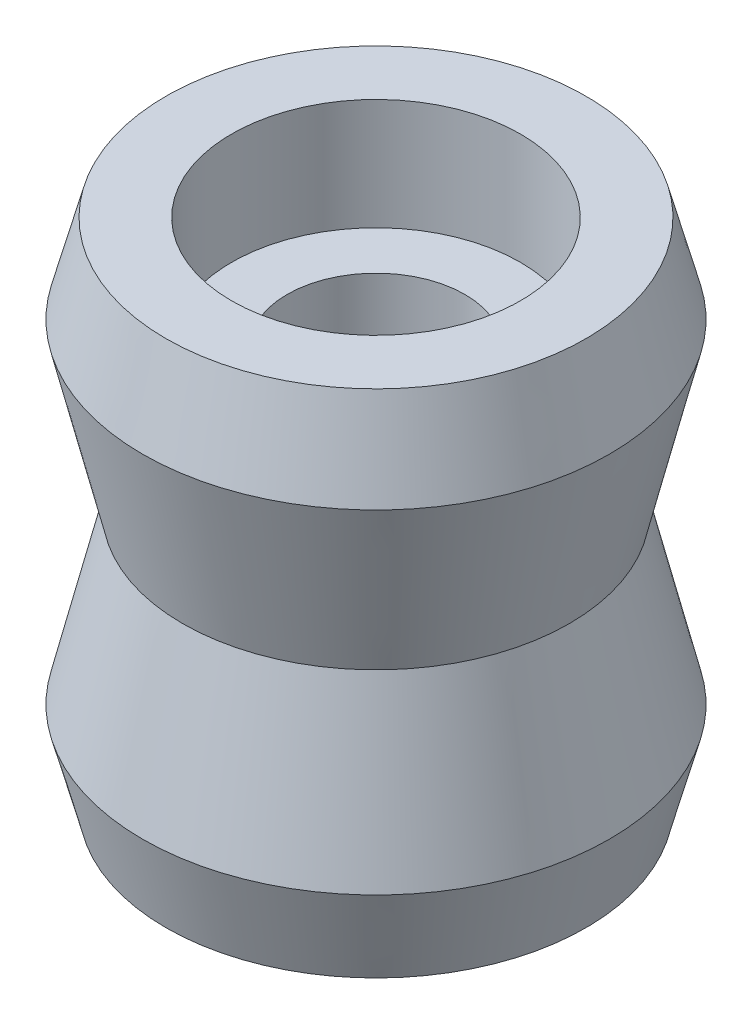
SolidWorks part; units mm, degrees
material "Maple"
ref_plane "Wasteboard" through (0, 0, 0) normal (0, 0, 1) x (1, 0, 0)
ref_plane "Left-Right" through (0, 0, 0) normal (0, 1, 0) x (1, 0, 0)
ref_plane "Front-Back" through (0, 0, 0) normal (1, 0, 0) x (0, 0, -1)
sketch "Sketch1" plane through (0, 0, 0) normal (0, 0, 1) x (1, 0, 0)
  line L0 (0, 42.3235) -> (0, -39.784) construction
  line L1 (0, -55) -> (0, 55) construction
  line L2 (0, 3.1923) -> (41.4814, 3.1923) construction
  line L3 (41.4814, 3.1923) -> (41.4814, 18.1923) construction
  line L4 (31.9163, 3.1923) -> (31.9163, 10.1923) construction
  line L5 (0, 30.7268) -> (2.5, 30.7268) construction
  line L6 (0, 37.5678) -> (4, 37.5678) construction
  line L7 (0, 43.5419) -> (6.5, 43.5419) construction
  line L8 (4, -3.2844) -> (4, 9.669)
  line L9 (4, 9.669) -> (6.5, 9.669)
  line L10 (6.5, 9.669) -> (6.5, 14.669)
  line L11 (6.5, 14.669) -> (9.4483, 14.669)
  line L12 (9.4483, 14.669) -> (10.5, 10.6923)
  line L13 (10.5, 10.6923) -> (8.7, 3.1923)
  line L14 (10.5, -4.3077) -> (8.7, 3.1923)
  line L15 (9.4483, -8.2844) -> (10.5, -4.3077)
  line L16 (6.5, -8.2844) -> (9.4483, -8.2844)
  line L17 (6.5, -3.2844) -> (6.5, -8.2844)
  line L18 (4, -3.2844) -> (6.5, -3.2844)
  line L19 (29.6361, 3.1923) -> (29.6361, 14.6923) construction
  line L20 (29.6361, 14.6923) -> (-14.8373, 14.6923) construction
  line L21 (10.5, 10.6923) -> (8.5155, 18.1962) construction
  point P18 (0, 0)
  point P25 (4, 3.1923)
  dimension "D1" = 15
  dimension "D2" = 7
  dimension "D3" = 4
  dimension "D4" = 2.5
  dimension "D5" = 6.5
  dimension "D6" = 6.5
  dimension "D7" = 7.5
  dimension "D9" = 2.5
  dimension "D10" = 82.1075
  dimension "D11" = 5
  dimension "D13" = 11.5
  dimension "D14" = 4.7
revolve "Revolve1" add sketch "Sketch1" angle 360 about L0
sketch "Sketch2" plane through (0, -3.2844, 0) normal (0, -1, 0) x (1, 0, 0)
  circle A0 centre (0, 0) radius 4
extrude "Boss-Extrude1" add sketch "Sketch2" against normal blind 0.2
